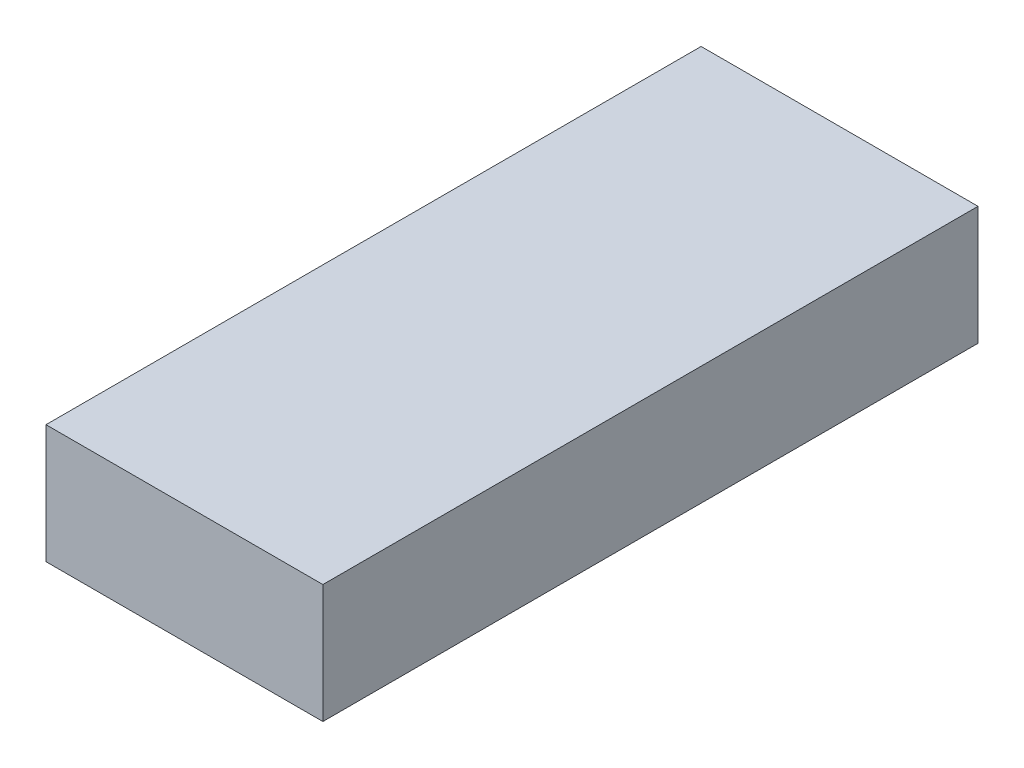
SolidWorks part; units mm, degrees
material "Pine"
ref_plane "Front Plane" through (0, 0, 0) normal (0, 0, 1) x (1, 0, 0)
ref_plane "Top Plane" through (0, 0, 0) normal (0, 1, 0) x (1, 0, 0)
ref_plane "Right Plane" through (0, 0, 0) normal (1, 0, 0) x (0, 0, -1)
sketch "Sketch1" plane through (0, 0, 0) normal (0, 0, 1) x (1, 0, 0)
  line L1 (-8.9932, 41.4962) -> (79.9068, 41.4962)
  line L2 (-8.9932, 41.4962) -> (-8.9932, 3.3962)
  line L3 (-8.9932, 3.3962) -> (79.9068, 3.3962)
  line L4 (79.9068, 41.4962) -> (79.9068, 3.3962)
  dimension "D1" = 88.9
  dimension "D2" = 38.1
extrude "Boss-Extrude1" add sketch "Sketch1" along normal blind 210.3438
